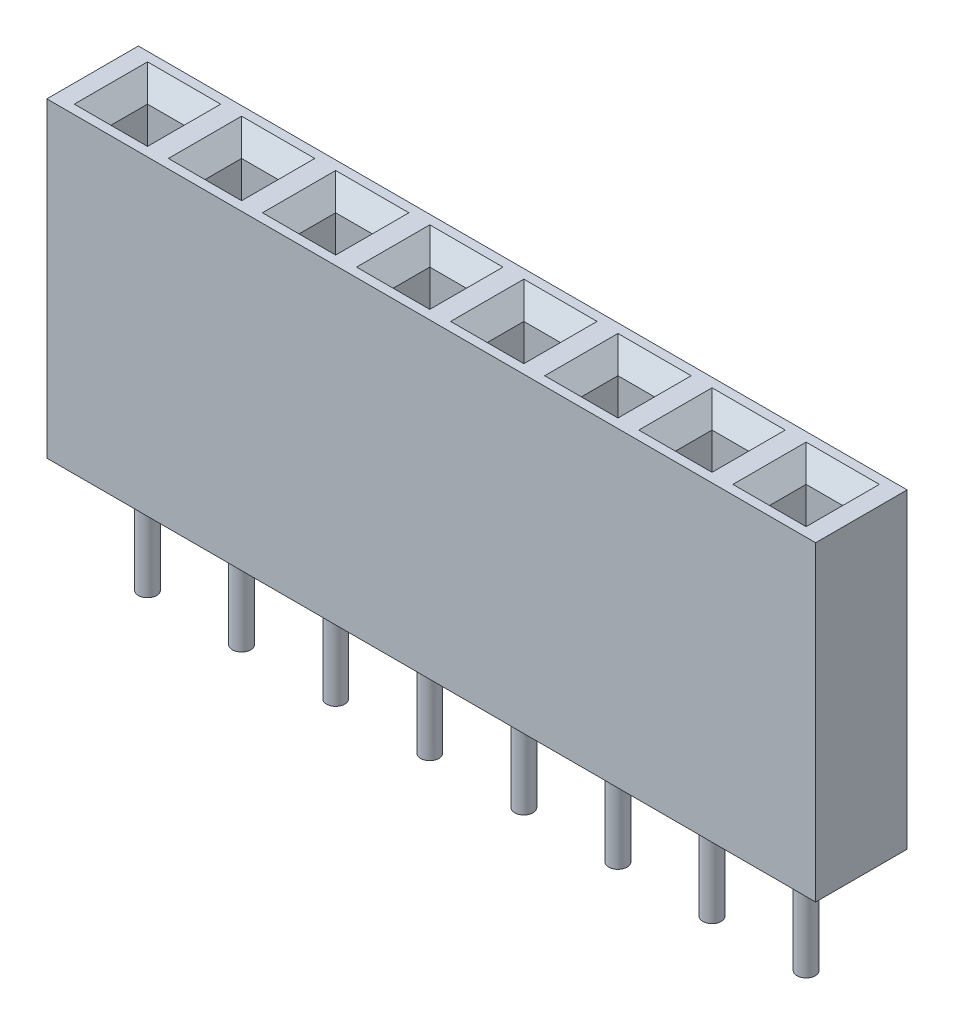
SolidWorks part; units mm, degrees
ref_plane "Front" through (0, 0, 0) normal (0, 0, 1) x (1, 0, 0)
ref_plane "Top" through (0, 0, 0) normal (0, 1, 0) x (1, 0, 0)
ref_plane "Right" through (0, 0, 0) normal (1, 0, 0) x (0, 0, -1)
sketch "Sketch1" plane through (0, 0, 0) normal (0, 1, 0) x (1, 0, 0)
  line L1 (0, 0) -> (21, 0)
  line L2 (0, 0) -> (0, 2.5)
  line L3 (0, 2.5) -> (21, 2.5)
  line L4 (21, 0) -> (21, 2.5)
  dimension "D1" = 2.5
  dimension "D2" = 21
extrude "Boss-Extrude1" add sketch "Sketch1" along normal blind 8.5
sketch "Sketch2" plane through (0, 8.5, 0) normal (0, 1, 0) x (1, 0, 0)
  line L0 (0, 1.25) -> (21, 1.25) construction
  line L1 (1, 1.75) -> (2, 1.75)
  line L2 (1, 1.75) -> (1, 0.75)
  line L3 (1, 0.75) -> (2, 0.75)
  line L4 (2, 1.75) -> (2, 0.75)
  line L5 (0, 2.5) -> (0, 0) construction
  line L6 (21, 0) -> (21, 2.5) construction
  line L7 (1, 1.25) -> (2, 1.25) construction
  line L8 (3.57, 1.75) -> (4.57, 1.75)
  line L9 (3.57, 1.75) -> (3.57, 0.75)
  line L10 (3.57, 0.75) -> (4.57, 0.75)
  line L11 (4.57, 1.75) -> (4.57, 0.75)
  line L12 (6.14, 1.75) -> (7.14, 1.75)
  line L13 (6.14, 1.75) -> (6.14, 0.75)
  line L14 (6.14, 0.75) -> (7.14, 0.75)
  line L15 (7.14, 1.75) -> (7.14, 0.75)
  line L16 (8.71, 1.75) -> (9.71, 1.75)
  line L17 (8.71, 1.75) -> (8.71, 0.75)
  line L18 (8.71, 0.75) -> (9.71, 0.75)
  line L19 (9.71, 1.75) -> (9.71, 0.75)
  line L20 (11.28, 1.75) -> (12.28, 1.75)
  line L21 (11.28, 1.75) -> (11.28, 0.75)
  line L22 (11.28, 0.75) -> (12.28, 0.75)
  line L23 (12.28, 1.75) -> (12.28, 0.75)
  line L24 (13.85, 1.75) -> (14.85, 1.75)
  line L25 (13.85, 1.75) -> (13.85, 0.75)
  line L26 (13.85, 0.75) -> (14.85, 0.75)
  line L27 (14.85, 1.75) -> (14.85, 0.75)
  line L28 (16.42, 1.75) -> (17.42, 1.75)
  line L29 (16.42, 1.75) -> (16.42, 0.75)
  line L30 (16.42, 0.75) -> (17.42, 0.75)
  line L31 (17.42, 1.75) -> (17.42, 0.75)
  line L32 (18.99, 1.75) -> (19.99, 1.75)
  line L33 (18.99, 1.75) -> (18.99, 0.75)
  line L34 (18.99, 0.75) -> (19.99, 0.75)
  line L35 (19.99, 1.75) -> (19.99, 0.75)
  dimension "D1" = 1
  dimension "D2" = 1
  dimension "D3" = 1
  dimension "D4" = 8
extrude "Cut-Extrude1" cut sketch "Sketch2" against normal blind 5
chamfer "Chamfer1" distance 0.5 angle 45 32 edges at (19.99, 8.5, -1.25) (19.49, 8.5, -1.75) (18.99, 8.5, -1.25) (19.49, 8.5, -0.75) (17.42, 8.5, -1.25) (16.92, 8.5, -1.75) (16.42, 8.5, -1.25) (16.92, 8.5, -0.75) (14.85, 8.5, -1.25) (14.35, 8.5, -1.75) (13.85, 8.5, -1.25) (14.35, 8.5, -0.75) (12.28, 8.5, -1.25) (11.78, 8.5, -1.75) (11.28, 8.5, -1.25) (11.78, 8.5, -0.75) (9.71, 8.5, -1.25) (9.21, 8.5, -1.75) (8.71, 8.5, -1.25) (9.21, 8.5, -0.75) (7.14, 8.5, -1.25) (6.64, 8.5, -1.75) (6.14, 8.5, -1.25) (6.64, 8.5, -0.75) (4.57, 8.5, -1.25) (4.07, 8.5, -1.75) (3.57, 8.5, -1.25) (4.07, 8.5, -0.75) (2, 8.5, -1.25) (1.5, 8.5, -1.75) (1, 8.5, -1.25) (1.5, 8.5, -0.75)
sketch "Sketch4" plane through (0, 3.5, 0) normal (0, 1, 0) x (1, 0, 0)
  line L0 (1, 0.75) -> (2, 1.75) construction
  line L1 (3.57, 0.75) -> (4.57, 1.75) construction
  line L2 (6.14, 0.75) -> (7.14, 1.75) construction
  line L3 (8.71, 0.75) -> (9.71, 1.75) construction
  line L4 (11.28, 0.75) -> (12.28, 1.75) construction
  line L5 (13.85, 0.75) -> (14.85, 1.75) construction
  line L6 (16.42, 0.75) -> (17.42, 1.75) construction
  line L7 (18.99, 0.75) -> (19.99, 1.75) construction
  circle A0 centre (1.5, 1.25) radius 0.25
  circle A1 centre (4.07, 1.25) radius 0.25
  circle A2 centre (6.64, 1.25) radius 0.25
  circle A3 centre (9.21, 1.25) radius 0.25
  circle A4 centre (11.78, 1.25) radius 0.25
  circle A5 centre (14.35, 1.25) radius 0.25
  circle A6 centre (16.92, 1.25) radius 0.25
  circle A7 centre (19.49, 1.25) radius 0.25
  dimension "D1" = 0.5
extrude "Boss-Extrude2" add sketch "Sketch4" against normal blind 6.5
